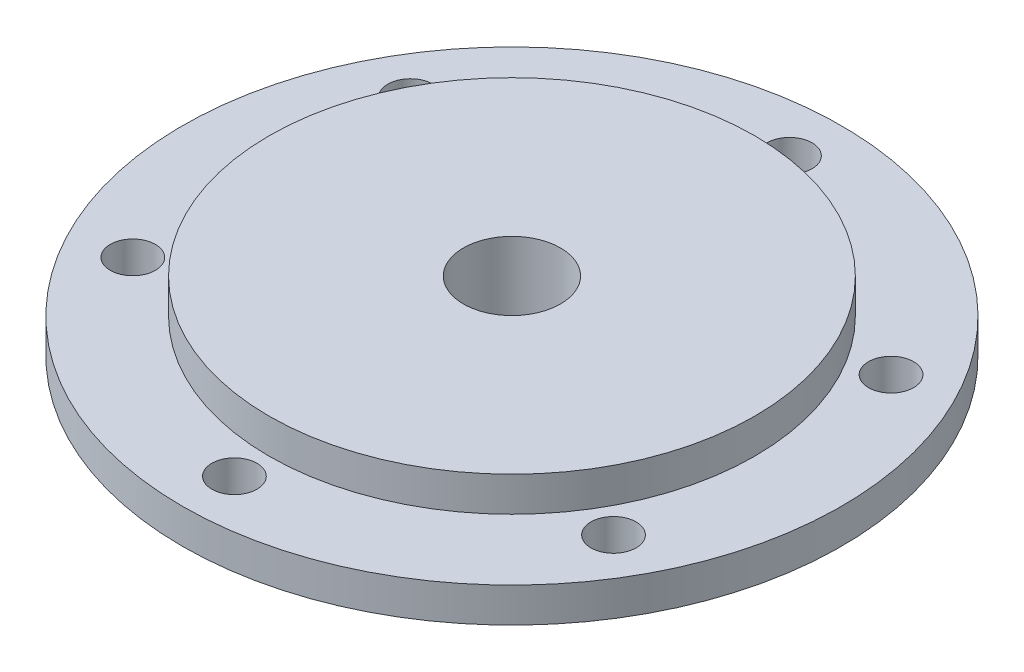
SolidWorks part; units mm, degrees
ref_plane "Front Plane" through (0, 0, 0) normal (0, 0, 1) x (1, 0, 0)
ref_plane "Top Plane" through (0, 0, 0) normal (0, 1, 0) x (1, 0, 0)
ref_plane "Right Plane" through (0, 0, 0) normal (1, 0, 0) x (0, 0, -1)
sketch "Sketch2" plane through (0, 0, 0) normal (0, 1, 0) x (1, 0, 0)
  circle A0 centre (0, 0) radius 47.5
  circle A1 centre (0, 0) radius 40 construction
  circle A2 centre (0, 40) radius 3.25
  circle A3 centre (34.641, 20) radius 3.25
  circle A4 centre (34.641, -20) radius 3.25
  circle A5 centre (0, -40) radius 3.25
  circle A6 centre (-34.641, -20) radius 3.25
  circle A7 centre (-34.641, 20) radius 3.25
  dimension "D1" = 80
  dimension "D2" = 95
  dimension "D3" = 6.5
  dimension "D4" = 6
extrude "Boss-Extrude1" add sketch "Sketch2" along normal mid plane 5
sketch "Sketch3" plane through (0, 2.5, 0) normal (0, 1, 0) x (1, 0, 0)
  circle A0 centre (0, 0) radius 7
  dimension "D1" = 14
extrude "Cut-Extrude1" cut sketch "Sketch3" against normal blind 5
sketch "Sketch4" plane through (0, 2.5, 0) normal (0, 1, 0) x (1, 0, 0)
  circle A0 centre (0, 0) radius 35
  dimension "D1" = 70
extrude "Boss-Extrude2" add sketch "Sketch4" along normal blind 5
sketch "Sketch5" plane through (0, -2.5, 0) normal (0, -1, 0) x (1, 0, 0)
  circle A0 centre (0, 0) radius 14
  dimension "D1" = 28
extrude "Boss-Extrude3" add sketch "Sketch5" along normal blind 18
sketch "Sketch6" plane through (0, -20.5, 0) normal (0, -1, 0) x (1, 0, 0)
  circle A0 centre (0, 0) radius 7
  dimension "D1" = 14
extrude "Cut-Extrude2" cut sketch "Sketch6" against normal through all both and the other way through all
fillet "Fillet1" radius 5 1 edges at (0, -2.5, 14)
